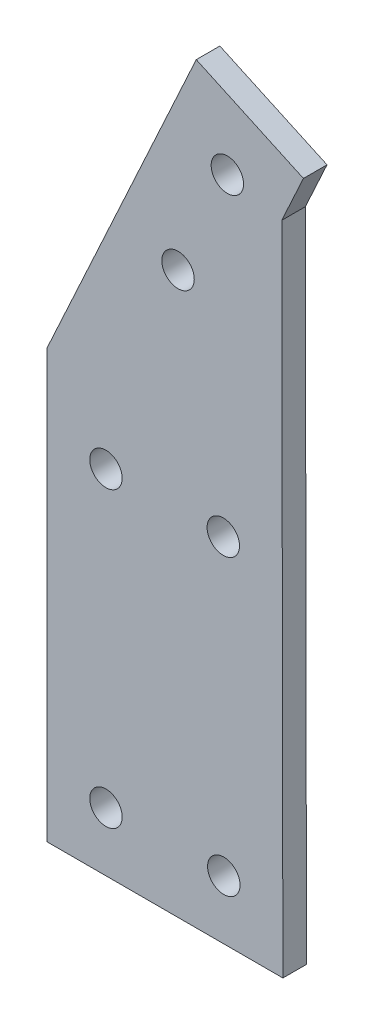
SolidWorks part; units mm, degrees
material "ABS"
ref_plane "Front Plane" through (0, 0, 0) normal (0, 0, 1) x (1, 0, 0)
ref_plane "Top Plane" through (0, 0, 0) normal (0, 1, 0) x (1, 0, 0)
ref_plane "Right Plane" through (0, 0, 0) normal (1, 0, 0) x (0, 0, -1)
sketch "Sketch1" plane through (0, 0, 0) normal (0, 0, 1) x (1, 0, 0)
  line L0 (0, 0) -> (18.1686, -8.3606)
  line L1 (18.1686, -8.3606) -> (14.4942, -16.3458)
  line L2 (14.4942, -16.3458) -> (14.6882, -127.5056)
  line L3 (14.6882, -127.5056) -> (-25.3118, -127.5056)
  line L4 (-25.3118, -127.5056) -> (-25.3118, -55.0056)
  line L5 (-25.3118, -55.0056) -> (0, 0)
  dimension "D1" = 20
  dimension "D2" = 60.55
  dimension "D3" = 72.5
  dimension "D4" = 40
  dimension "D5" = 111.16
  dimension "D6" = 8.79
  dimension "D7" = 90
extrude "Boss-Extrude1" add sketch "Sketch1" along normal blind 4
sketch "Sketch2" plane through (0, 0, 4) normal (0, 0, 1) x (1, 0, 0)
  line L0 (-25.3118, -55.0056) -> (-25.3118, -127.5056) construction
  line L1 (14.6882, -127.5056) -> (14.4942, -16.3458) construction
  line L2 (-25.3118, -127.5056) -> (14.6882, -127.5056) construction
  circle A0 centre (-15.3118, -117.5056) radius 2.75
  circle A1 centre (4.6707, -117.5056) radius 2.75
  circle A2 centre (-15.3118, -67.7556) radius 2.75
  circle A3 centre (4.5839, -67.7556) radius 2.75
  dimension "D1" = 5.5
  dimension "D2" = 5.5
  dimension "D7" = 5.5
  dimension "D8" = 5.5
  dimension "D3" = 10
  dimension "D4" = 10
  dimension "D5" = 10
  dimension "D6" = 10
  dimension "D10" = 49.75
  dimension "D11" = 10
  dimension "D12" = 10
extrude "Cut-Extrude1" cut sketch "Sketch2" against normal blind 4
sketch "Sketch3" plane through (0, 0, 4) normal (0, 0, 1) x (1, 0, 0)
  line L0 (0, 0) -> (-25.3118, -55.0056) construction
  line L2 (18.1686, -8.3606) -> (0, 0) construction
  line L3 (5.2718, -14.2595) -> (-3.0888, -32.4281) construction
  circle A0 centre (5.2718, -14.2595) radius 2.75
  circle A1 centre (-3.0888, -32.4281) radius 2.75
  dimension "D1" = 5.5
  dimension "D6" = 5.5
  dimension "D2" = 10.75
  dimension "D3" = 10.75
  dimension "D4" = 20
  dimension "D5" = 10.75
extrude "Cut-Extrude2" cut sketch "Sketch3" against normal blind 4
